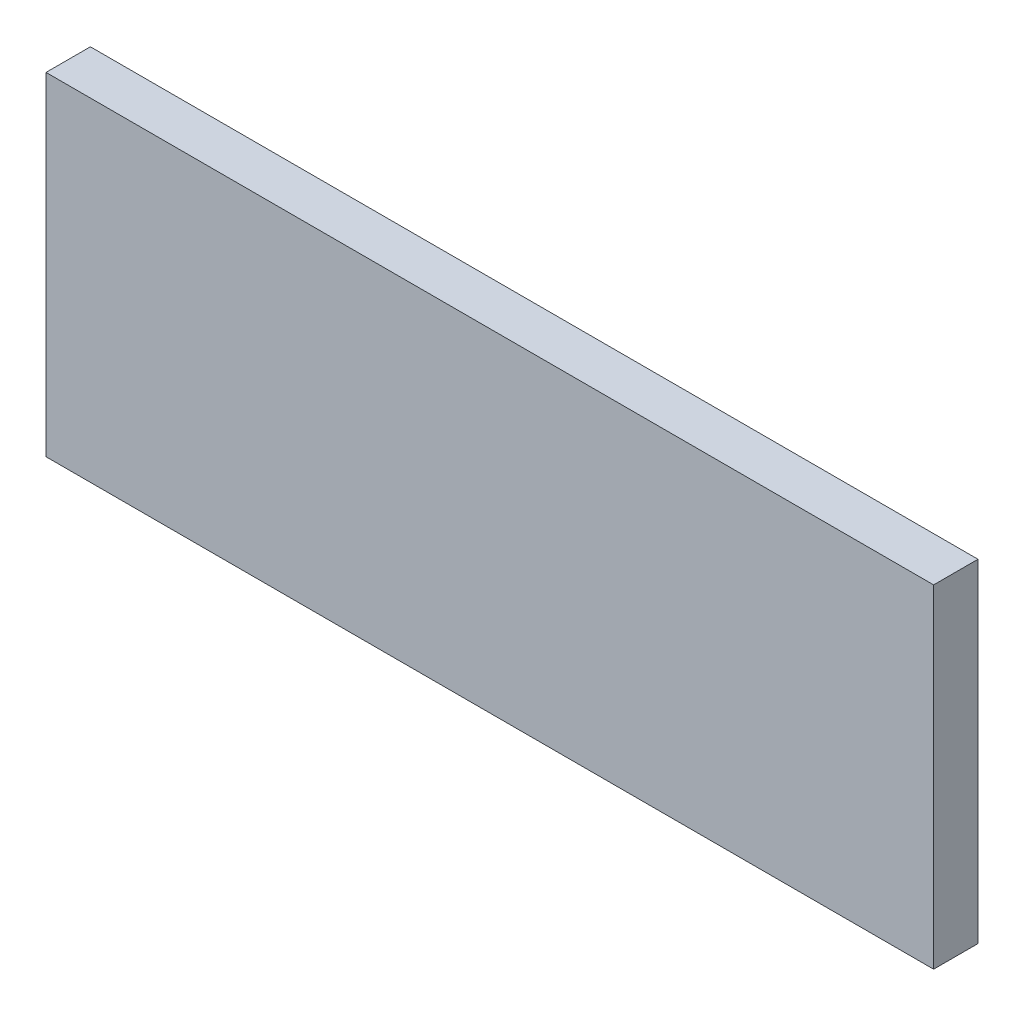
SolidWorks part; units mm, degrees
ref_plane "Front Plane" through (0, 0, 0) normal (0, 0, 1) x (1, 0, 0)
ref_plane "Top Plane" through (0, 0, 0) normal (0, 1, 0) x (1, 0, 0)
ref_plane "Right Plane" through (0, 0, 0) normal (1, 0, 0) x (0, 0, -1)
sketch "Sketch1" plane through (0, 0, 0) normal (0, 0, 1) x (1, 0, 0)
  line L1 (-40, 15) -> (40, 15)
  line L2 (-40, 15) -> (-40, -15)
  line L3 (-40, -15) -> (40, -15)
  line L4 (40, 15) -> (40, -15)
extrude "Boss-Extrude1" add sketch "Sketch1" along normal blind 4 contours L1 L4 L3 L2
ref_plane "Plane1" through (0, 0, 3.5) normal (0, 0, 1) x (1, 0, 0)
sketch "Sketch12" plane through (0, -5, 0) normal (0, 0, 1) x (1, 0, 0)
  line L0 (-35, 12.5) -> (32.5, 12.5)
  line L1 (-35, 12.5) -> (-35, -2.5)
  line L2 (-32.5, -2.5) -> (35, -2.5)
  line L3 (35, -2.5) -> (35, 12.5)
  line L5 (32.5, 12.5) -> (-35, -2.5)
  line L6 (35, 12.5) -> (-32.5, -2.5)
sketch "Sketch13" plane through (0, 0, 0) normal (0, 0, 1) x (1, 0, 0)
  line L0 (-40, 15) -> (40, 15) construction
  line L1 (-35, 15) -> (-32.5, 15)
  line L2 (-35, 15) -> (-35, 5)
  line L3 (-35, 5) -> (-32.5, 5)
  line L4 (-32.5, 15) -> (-32.5, 5)
  line L6 (30, 15) -> (32.5, 15)
  line L7 (30, 15) -> (30, 6.9444)
  line L9 (32.5, 15) -> (32.5, 7.5)
  line L10 (30, 6.9444) -> (32.5, 7.5)
  line L11 (-32.5, -7.5) -> (-32.5, -15)
  line L12 (-32.5, -15) -> (-30, -15)
  line L13 (-30, -6.9444) -> (-30, -15)
  line L14 (32.5, -5) -> (35, -5)
  line L15 (32.5, -5) -> (32.5, -15)
  line L16 (32.5, -15) -> (35, -15)
  line L17 (35, -5) -> (35, -15)
  line L18 (-40, -15) -> (40, -15) construction
  line L19 (-30, -6.9444) -> (-32.5, -7.5)
  line L20 (35, 7.5) -> (-32.5, -7.5) construction
  line L21 (32.5, 7.5) -> (-35, -7.5) construction
